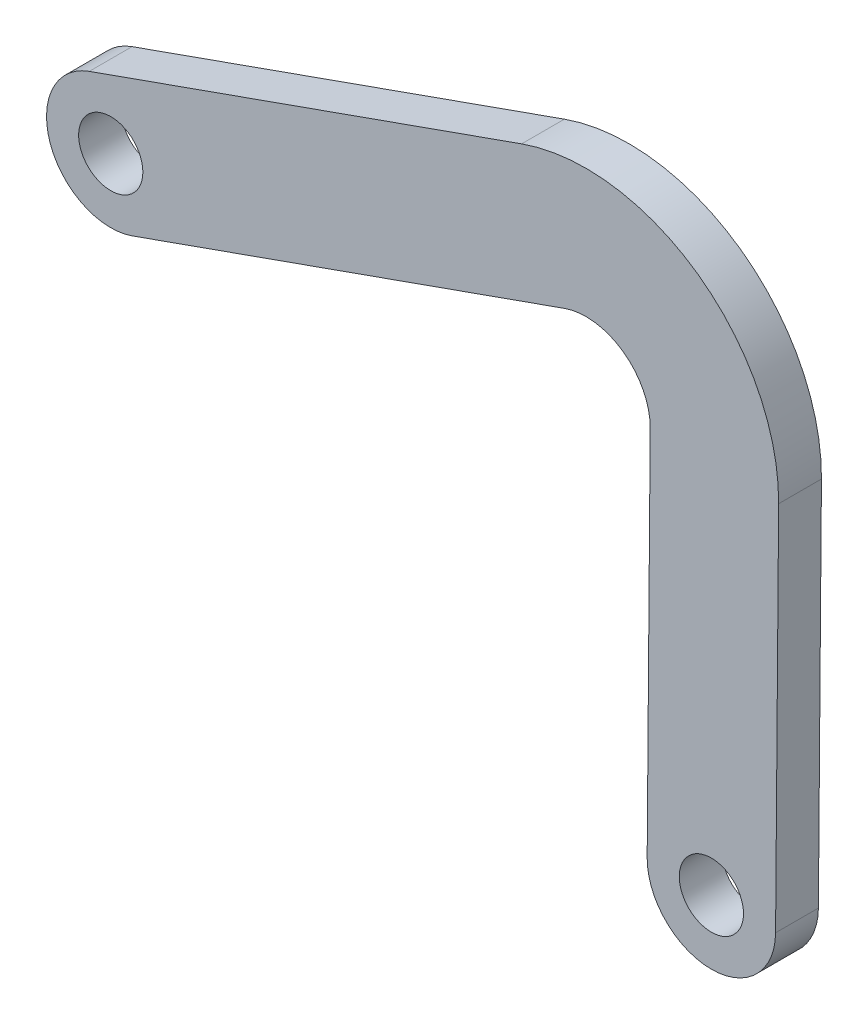
SolidWorks part; units mm, degrees
ref_plane "Piano frontale" through (0, 0, 0) normal (0, 0, 1) x (1, 0, 0)
ref_plane "Piano superiore" through (0, 0, 0) normal (0, 1, 0) x (1, 0, 0)
ref_plane "Piano destro" through (0, 0, 0) normal (1, 0, 0) x (0, 0, -1)
sketch "Schizzo1" plane through (0, 0, 0) normal (0, 0, 1) x (1, 0, 0)
  line L0 (-21.5809, 12.4204) -> (-1.3829, 19.5852)
  line L1 (10.6256, 11.0293) -> (10.4829, -6.4021)
  line L2 (4.4831, -6.3529) -> (4.6258, 11.0785)
  line L3 (-19.575, 6.7657) -> (0.623, 13.9304)
  line L4 (-20.578, 9.593) -> (7.6959, 19.6225) construction
  line L5 (7.6959, 19.6225) -> (7.483, -6.3775) construction
  arc A0 (4.4831, -6.3529) -> (10.4829, -6.4021) centre (7.483, -6.3775) ccw
  arc A1 (-19.575, 6.7657) -> (-21.5809, 12.4204) centre (-20.578, 9.593) cw
  arc A3 (4.6258, 11.0785) -> (0.623, 13.9304) centre (1.6259, 11.103) ccw
  arc A4 (10.6256, 11.0293) -> (-1.3829, 19.5852) centre (1.6259, 11.103) ccw
  dimension "D1" = 3
  dimension "D2" = 3
  dimension "D3" = 9
  dimension "D4" = 3
  dimension "D5" = 30
  dimension "D6" = 26
  dimension "D7" = 70
extrude "Estrusione-Estrusione1" add sketch "Schizzo1" along normal blind 2
sketch "Schizzo2" plane through (0, 0, 2) normal (0, 0, 1) x (1, 0, 0)
  circle A0 centre (7.483, -6.3775) radius 1.5
  circle A1 centre (-20.578, 9.593) radius 1.5
  dimension "D1" = 3
  dimension "D2" = 3
extrude "Taglio-Estrusione1" cut sketch "Schizzo2" against normal blind 2
